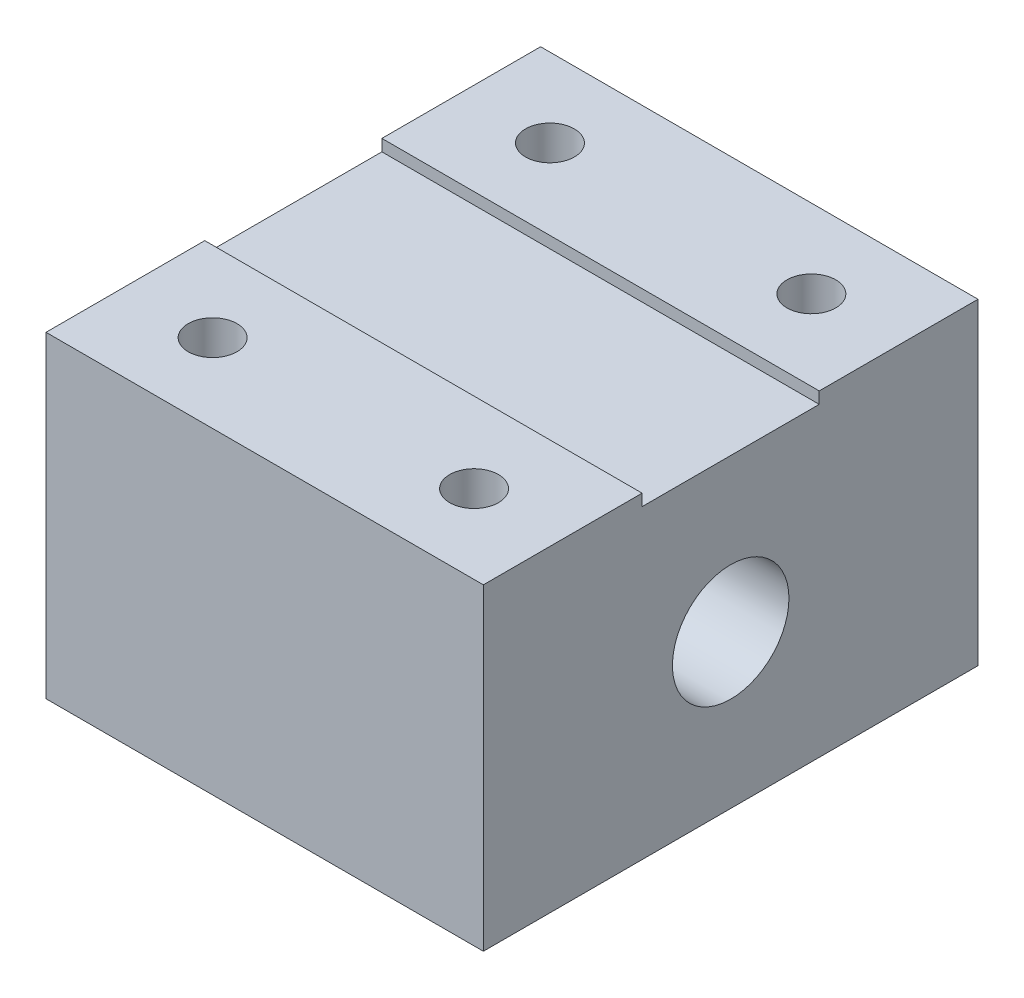
SolidWorks part; units mm, degrees
ref_plane "Front Plane" through (0, 0, 0) normal (0, 0, 1) x (1, 0, 0)
ref_plane "Top Plane" through (0, 0, 0) normal (0, 1, 0) x (1, 0, 0)
ref_plane "Right Plane" through (0, 0, 0) normal (1, 0, 0) x (0, 0, -1)
sketch "Sketch1" plane through (0, 0, 0) normal (0, 1, 0) x (1, 0, 0)
  line L0 (15.015, 33.96) -> (15.015, 0) construction
  line L1 (0, 0) -> (30.03, 0)
  line L2 (0, 0) -> (0, 33.96)
  line L3 (0, 33.96) -> (30.03, 33.96)
  line L4 (30.03, 0) -> (30.03, 33.96)
  line L5 (0, 28.56) -> (30.03, 28.56) construction
  line L6 (23.99, 33.96) -> (23.99, 0) construction
  line L7 (0, 16.98) -> (30.03, 16.98) construction
  circle A0 centre (23.99, 28.56) radius 1.675
  circle A1 centre (6.04, 28.56) radius 1.675
  circle A2 centre (23.99, 5.4) radius 1.675
  circle A3 centre (6.04, 5.4) radius 1.675
  dimension "D5" = 3.35
  dimension "D1" = 33.96
  dimension "D2" = 30.03
  dimension "D3" = 6.04
  dimension "D4" = 5.4
extrude "Boss-Extrude4" add sketch "Sketch1" along normal blind 21.79
sketch "Sketch5" plane through (30.03, 0, 0) normal (1, 0, 0) x (0, 0, -1)
  line L0 (33.96, 10.5) -> (0, 10.5) construction
  line L1 (33.96, 21.79) -> (33.96, 0) construction
  line L2 (0, 21.79) -> (0, 0) construction
  line L3 (0, 0) -> (33.96, 0) construction
  circle A0 centre (16.98, 10.5) radius 4
  dimension "D2" = 8
  dimension "D1" = 10.5
extrude "Cut-Extrude1" cut sketch "Sketch5" against normal through all
sketch "Sketch7" plane through (0, 21.79, 0) normal (0, 1, 0) x (1, 0, 0)
  line L0 (0, 33.96) -> (0, 0) construction
  line L1 (0, 23.06) -> (30.03, 23.06)
  line L2 (0, 23.06) -> (0, 10.9)
  line L3 (0, 10.9) -> (30.03, 10.9)
  line L4 (30.03, 23.06) -> (30.03, 10.9)
  line L5 (30.03, 33.96) -> (0, 33.96) construction
  line L6 (0, 0) -> (30.03, 0) construction
  line L7 (30.03, 0) -> (30.03, 33.96) construction
  dimension "D1" = 10.9
  dimension "D2" = 10.9
extrude "Cut-Extrude2" cut sketch "Sketch7" against normal blind 0.8
